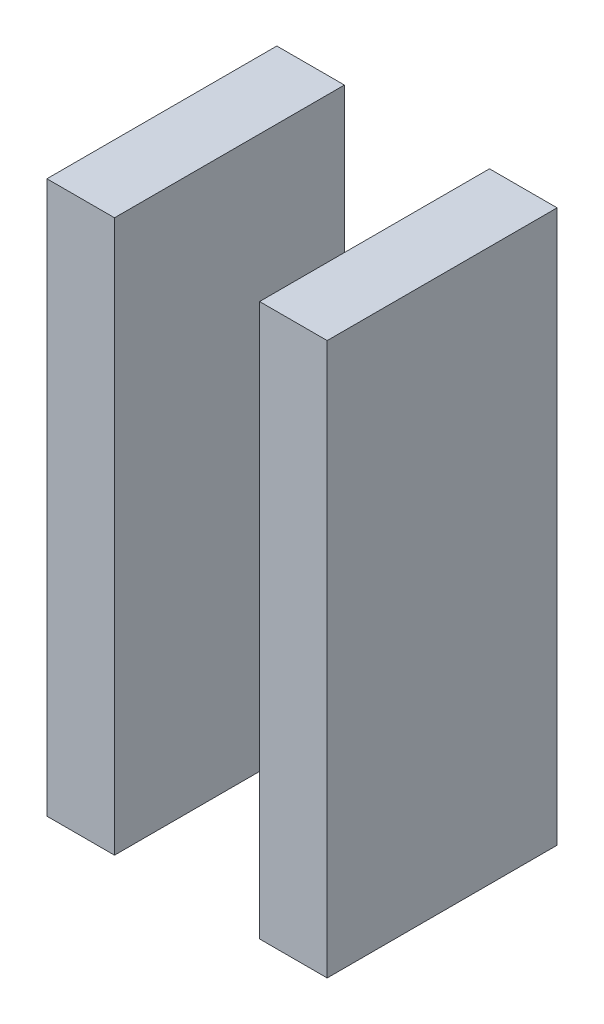
SolidWorks part; units mm, degrees
ref_plane "Ebene vorne" through (0, 0, 0) normal (0, 0, 1) x (1, 0, 0)
ref_plane "Ebene oben" through (0, 0, 0) normal (0, 1, 0) x (1, 0, 0)
ref_plane "Ebene rechts" through (0, 0, 0) normal (1, 0, 0) x (0, 0, -1)
sketch "Skizze1" plane through (0, 0, 0) normal (0, 0, 1) x (1, 0, 0)
  line L0 (194.515, -34.095) -> (192.485, -34.095) construction
  line L1 (192.03, -34.095) -> (194.97, -34.095)
  line L2 (192.03, -34.095) -> (192.03, -58.105)
  line L3 (192.03, -58.105) -> (194.97, -58.105)
  line L4 (194.97, -34.095) -> (194.97, -58.105)
  line L5 (192.485, -58.105) -> (194.515, -58.105) construction
  line L6 (198.125, -34.914) -> (198.125, -44.9366) construction
  line L7 (201.28, -34.095) -> (201.28, -58.105)
  line L8 (204.22, -58.105) -> (201.28, -58.105)
  line L9 (204.22, -34.095) -> (204.22, -58.105)
  line L10 (204.22, -34.095) -> (201.28, -34.095)
  arc A0 (192.485, -34.095) -> (192.485, -35.005) centre (192.485, -34.55) ccw construction
  arc A1 (194.515, -39.705) -> (194.515, -38.795) centre (194.515, -39.25) ccw construction
  arc A2 (201.735, -34.095) -> (201.735, -35.005) centre (201.735, -34.55) ccw construction
extrude "Aufsatz-Linear austragen1" add sketch "Skizze1" along normal blind 10 from offset 1
